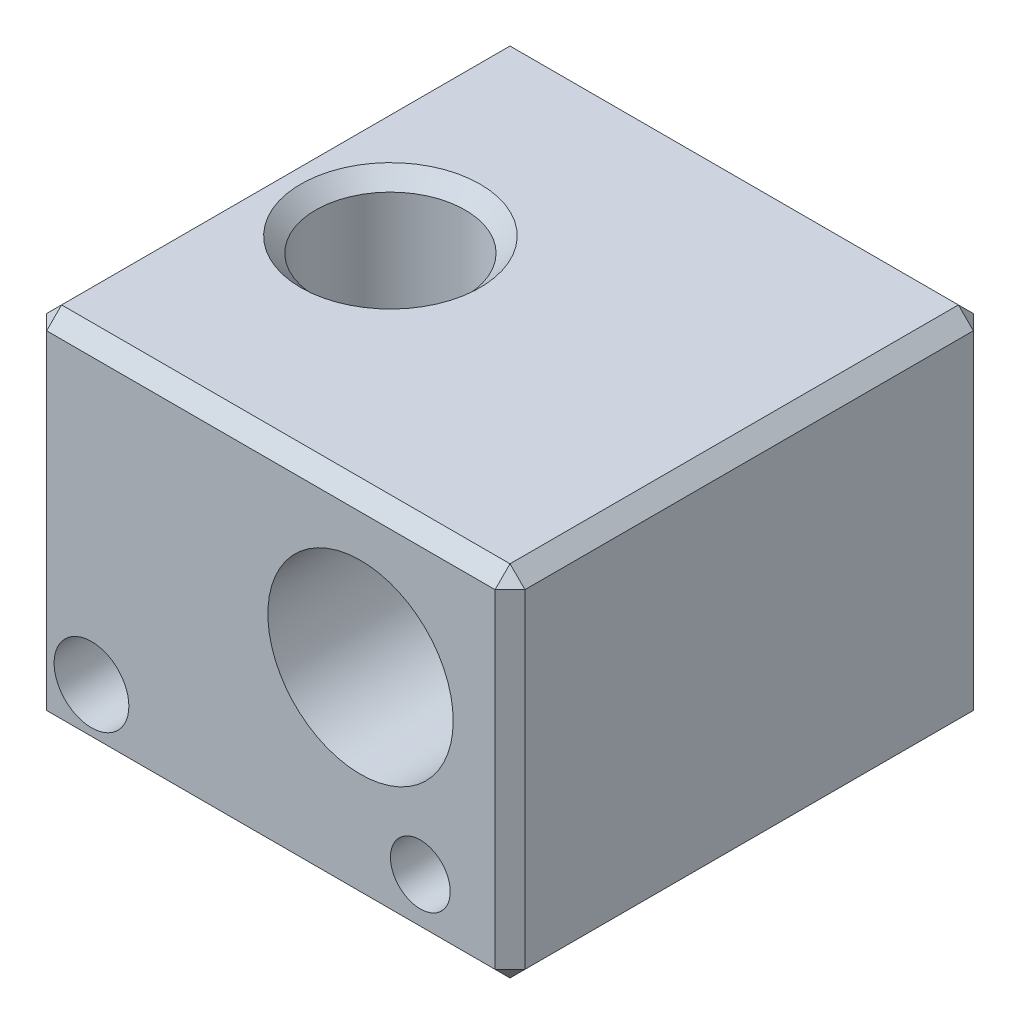
SolidWorks part; units mm, degrees
material "AISI 316 Annealed Stainless Steel Bar (SS)"
ref_plane "Front Plane" through (0, 0, 0) normal (0, 0, 1) x (1, 0, 0)
ref_plane "Top Plane" through (0, 0, 0) normal (0, 1, 0) x (1, 0, 0)
ref_plane "Right Plane" through (0, 0, 0) normal (1, 0, 0) x (0, 0, -1)
sketch "Sketch1" plane through (0, 0, 0) normal (0, 1, 0) x (1, 0, 0)
  line L1 (-8, -8) -> (8, -8)
  line L2 (-8, -8) -> (-8, 8)
  line L3 (-8, 8) -> (8, 8)
  line L4 (8, -8) -> (8, 8)
  line L5 (-8, -8) -> (8, 8) construction
  line L6 (-8, 8) -> (8, -8) construction
  point P0 (0, 0)
  dimension "D1" = 16
  dimension "D2" = 16
extrude "Boss-Extrude1" add sketch "Sketch1" along normal blind 12 contours L2 L3 L4 L1
sketch "Sketch2" plane through (0, 0, 8) normal (0, 0, 1) x (1, 0, 0)
  line L0 (-8, 12) -> (-8, 0) construction
  line L1 (-8, 0) -> (8, 0) construction
  circle A0 centre (3, 7) radius 3.1
  circle A1 centre (5, 2) radius 1
  point P10 (6.0564, 0)
  dimension "D2" = 6.2
  dimension "D4" = 13
  dimension "D6" = 2
  dimension "D1" = 11
  dimension "D3" = 7
  dimension "D5" = 2
extrude "Cut-Extrude1" cut sketch "Sketch2" against normal through all
hole_wizard "Ø2.5 (2.5) Diameter Hole1" positions "Sketch4" profile "Sketch3" hole size "Ø2.5" standard "ANSI Metric"
sketch "Sketch4" plane through (0, 0, 8) normal (0, 0, 1) x (1, 0, 0)
  line L0 (-8, 12) -> (-8, 0) construction
  line L1 (-8, 0) -> (8, 0) construction
  point P0 (-6, 2)
  dimension "D1" = 2
  dimension "D2" = 2
sketch "Sketch3" plane through (-6, 2, 8) normal (1, 0, 0) x (0, -1, 0)
  line L0 (0, 0) -> (0, 4.5)
  line L1 (0, 4.5) -> (1.25, 4.5)
  line L2 (1.25, 4.5) -> (1.25, 0)
  line L5 (1.25, 0) -> (0, 0)
  line L10 (0, 4.5) -> (-1.25, 4.5) construction
  line L11 (0, -6.35) -> (0, 107.95) construction
  dimension "Hole Dia." = 2.5
  dimension "Hole Depth" = 4.5
  dimension "Drill Angle" = 180
hole_wizard "Tap Drill for M6x1.0 Tap1" positions "Sketch7" profile "Sketch6" hole size "M6x1.0" standard "ANSI Metric" end condition through all
sketch "Sketch7" plane through (0, 12, 0) normal (0, 1, 0) x (1, 0, 0)
  line L0 (-8, -8) -> (-8, 8) construction
  point P0 (-4, 0)
  dimension "D1" = 4
sketch "Sketch6" plane through (-4, 12, 0) normal (1, 0, 0) x (0, 0, 1)
  line L0 (0, 0) -> (0, 12)
  line L1 (0, 12) -> (2.5, 12)
  line L2 (2.5, 12) -> (2.5, 0)
  line L5 (2.5, 0) -> (0, 0)
  line L11 (0, -6.35) -> (0, 107.95) construction
  dimension "Thru Hole Dia." = 5
  dimension "Thru Hole Depth" = 12
hole_wizard "Tap Drill for M3x0.5 Tap1" positions "Sketch9" profile "Sketch8" hole size "M3x0.5" standard "ANSI Metric"
sketch "Sketch9" plane through (0, 0, 0) normal (0, -1, 0) x (-1, 0, 0)
  line L0 (8, -8) -> (8, 8) construction
  point P0 (-2, 0)
  dimension "D1" = 10
sketch "Sketch8" plane through (2, 0, 0) normal (1, 0, 0) x (0, 0, -1)
  line L0 (0, 0) -> (0, 7.7501)
  line L1 (0, 7.7501) -> (1.25, 6.999)
  line L2 (1.25, 6.999) -> (1.25, 0)
  line L5 (1.25, 0) -> (0, 0)
  line L10 (0, 7.7501) -> (-1.25, 6.999) construction
  line L11 (0, -6.35) -> (0, 107.95) construction
  dimension "Hole Dia." = 2.5
  dimension "Hole Depth" = 6.999
  dimension "Drill Angle" = 118
chamfer "Chamfer1" distance 0.5 angle 45 15 edges at (-4, 0, 2.5) (2, 0, -1.25) (-8, 6, -8) (-8, 6, 8) (8, 6, 8) (8, 0, 0) (0, 0, 8) (-8, 0, 0) (0, 0, -8) (8, 6, -8) (-8, 12, 0) (0, 12, -8) (8, 12, 0) (0, 12, 8) (-4, 12, 2.5)
